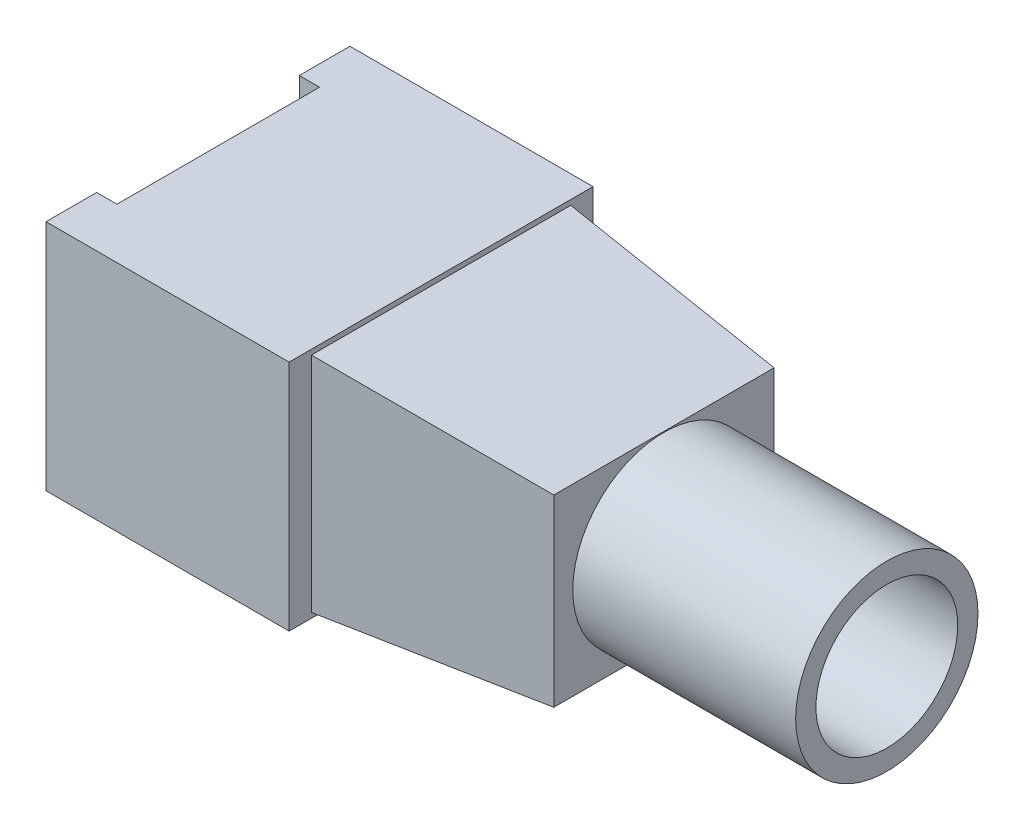
SolidWorks part; units mm, degrees
material "ABS"
ref_plane "Front Plane" through (0, 0, 0) normal (0, 0, 1) x (1, 0, 0)
ref_plane "Top Plane" through (0, 0, 0) normal (0, 1, 0) x (1, 0, 0)
ref_plane "Right Plane" through (0, 0, 0) normal (1, 0, 0) x (0, 0, -1)
sketch "Sketch2" plane through (0, 0, 0) normal (0, 1, 0) x (1, 0, 0)
  line L0 (-6, -5) -> (-6, -7.5)
  line L1 (-6, 7.5) -> (6, 7.5)
  line L2 (-6, 7.5) -> (-6, 5)
  line L3 (-6, -7.5) -> (6, -7.5)
  line L4 (6, 7.5) -> (6, -7.5)
  line L5 (-6, 7.5) -> (6, -7.5) construction
  line L6 (-6, -7.5) -> (6, 7.5) construction
  line L7 (-6, -5) -> (-5, -5)
  line L9 (-6, 5) -> (-5, 5)
  line L10 (-5, -5) -> (-5, 5)
  point P0 (0, 0)
  point P10 (-5, 0)
  dimension "D1" = 15
  dimension "D2" = 12
  dimension "D3" = 10
  dimension "D4" = 1
extrude "Boss-Extrude1" add sketch "Sketch2" along normal blind 11.5
sketch "Sketch4" plane through (6, 0, 0) normal (1, 0, 0) x (0, 0, -1)
  line L0 (-7.5, 11.5) -> (7.5, 11.5) construction
  line L1 (-6.4, 11.25) -> (6.4, 11.25)
  line L2 (-6.4, 11.25) -> (-6.4, 0.25)
  line L3 (-6.4, 0.25) -> (6.4, 0.25)
  line L4 (6.4, 11.25) -> (6.4, 0.25)
  line L5 (-6.4, 11.25) -> (6.4, 0.25) construction
  line L6 (-6.4, 0.25) -> (6.4, 11.25) construction
  line L7 (7.5, 11.5) -> (7.5, 0) construction
  point P0 (0, 5.75)
  point P5 (0, 11.25)
  point P8 (0, 11.5)
  point P9 (6.4, 5.75)
  point P12 (7.5, 5.75)
  dimension "D1" = 12.8
  dimension "D2" = 11
extrude "Boss-Extrude2" add sketch "Sketch4" along normal blind 11 draft 5
sketch "Sketch5" plane through (17, 0, 0) normal (1, 0, 0) x (0, 0, -1)
  line L0 (-5.4376, 1.2124) -> (5.4376, 1.2124) construction
  line L1 (5.4376, 1.2124) -> (5.4376, 10.2876) construction
  circle A0 centre (0, 5.75) radius 4.5
  circle A1 centre (0, 5.75) radius 3.5
  point P5 (0, 1.2124)
  point P10 (5.4376, 5.75)
  dimension "D1" = 9
  dimension "D2" = 1
extrude "Boss-Extrude3" add sketch "Sketch5" along normal blind 11
